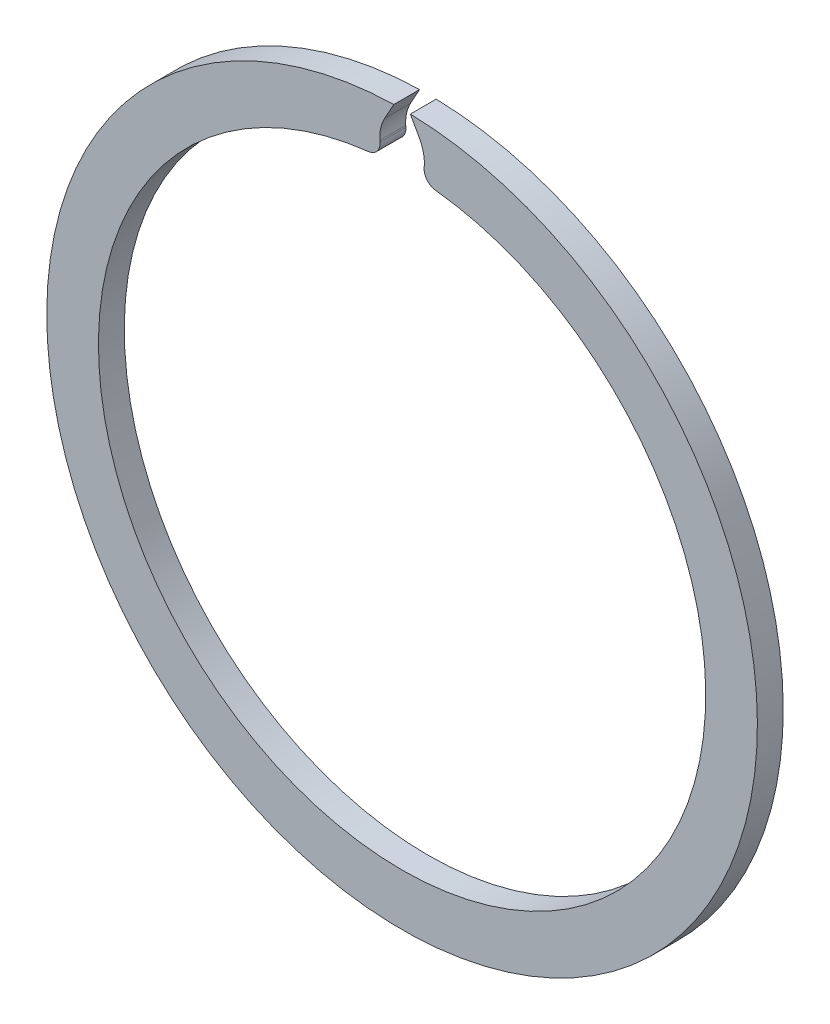
SolidWorks part; units mm, degrees
material "1.0037 (S235JR)"
ref_plane "Piano frontale" through (0, 0, 0) normal (0, 0, 1) x (1, 0, 0)
ref_plane "Piano superiore" through (0, 0, 0) normal (0, 1, 0) x (1, 0, 0)
ref_plane "Piano destro" through (0, 0, 0) normal (1, 0, 0) x (0, 0, -1)
sketch "Schizzo1" plane through (0, 0, 0) normal (0, 0, 1) x (1, 0, 0)
  line L0 (0, 0) -> (0, 27.5) construction
  line L1 (-1.7076, 24.42) -> (-1.7168, 24.5514)
  line L2 (-1.348, 26.2151) -> (-0.6399, 27.4926)
  line L3 (1.348, 26.2151) -> (0.6399, 27.4926)
  line L4 (1.7076, 24.42) -> (1.7168, 24.5514)
  arc A0 (-2.5948, 23.3563) -> (2.5948, 23.3563) centre (0, 0) ccw
  arc A1 (-0.6399, 27.4926) -> (0.6399, 27.4926) centre (0, 0) ccw
  circle A2 centre (0, 0) radius 25.5 construction
  arc A3 (-1.7076, 24.42) -> (-2.5948, 23.3563) centre (-2.7052, 24.3502) cw
  circle A4 centre (0, 0) radius 23.5 construction
  arc A5 (-1.348, 26.2151) -> (-1.7168, 24.5514) centre (1.2759, 24.7607) ccw
  arc A6 (1.7076, 24.42) -> (2.5948, 23.3563) centre (2.7052, 24.3502) ccw
  arc A7 (1.348, 26.2151) -> (1.7168, 24.5514) centre (-1.2759, 24.7607) cw
  point P4 (22.4732, 6.8707)
  point P14 (-1.6393, 23.4428)
  point P17 (-1.7788, 25.4379)
  dimension "D1" = 47
  dimension "D2" = 55
  dimension "D7" = 1
  dimension "D8" = 3
  dimension "D4" = 4
  dimension "D5" = 2
  dimension "D6" = 33
  dimension "D3" = 2
extrude "Estrusione-Estrusione1" add sketch "Schizzo1" along normal blind 2
